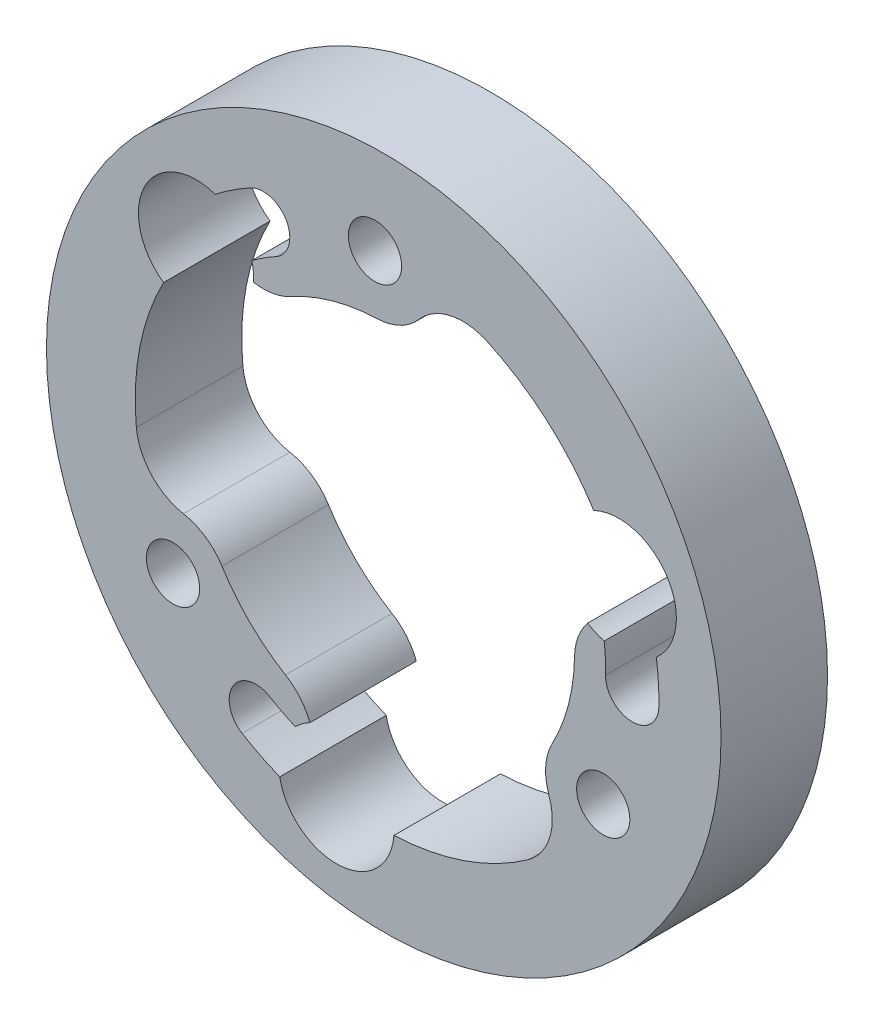
SolidWorks part; units mm, degrees
ref_plane "Plan de face" through (0, 0, 0) normal (0, 0, 1) x (1, 0, 0)
ref_plane "Plan de dessus" through (0, 0, 0) normal (0, 1, 0) x (1, 0, 0)
ref_plane "Plan de droite" through (0, 0, 0) normal (1, 0, 0) x (0, 0, -1)
sketch "Esquisse1" plane through (0, 0, 0) normal (0, 0, 1) x (1, 0, 0)
  line L0 (-0.4938, 13.9913) -> (-11.8699, -7.4233) construction
  line L1 (-11.8699, -7.4233) -> (12.3637, -6.568) construction
  line L2 (12.3637, -6.568) -> (-0.4938, 13.9913) construction
  circle A0 centre (0, 0) radius 19
  circle A2 centre (-0.4938, 13.9913) radius 1.5
  arc A12 (-0.3792, 10.7433) -> (1.9825, 11.8865) centre (-0.4938, 13.9913) ccw
  arc A16 (5.8069, 12.7389) -> (1.9825, 11.8865) centre (4.4589, 9.7817) ccw
  arc A18 (-12.4014, 6.4965) -> (-13.9357, -1.3405) centre (0, 0) ccw
  arc A27 (0.5746, -13.9882) -> (8.1288, -11.3984) centre (0, 0) ccw
  arc A28 (11.8268, 7.4917) -> (5.8069, 12.7389) centre (0, 0) ccw
  arc A30 (-6.0642, 10.9305) -> (-7.5196, 13.5538) centre (-6.7919, 12.2421) ccw
  arc A31 (-7.3226, 9.0358) -> (-5.2152, 9.4002) centre (-6.7919, 12.2421) ccw
  circle A34 centre (-0.4938, 13.9913) radius 3.25 construction
  arc A35 (-7.3226, 9.0358) -> (-10.0387, 12.3873) centre (-6.7919, 12.2421) ccw construction
  arc A36 (-0.6094, 13.9867) -> (-1.9502, 13.6321) centre (-0.4679, 10.7398) ccw [skipped]
  arc A38 (-0.3792, 10.7433) -> (-5.2152, 9.4002) centre (0, 0) ccw
  arc A41 (-7.3226, 9.0358) -> (-7.4369, 10.047) centre (-10.5694, 9.1809) ccw
  arc A47 (-9.4978, 12.2492) -> (-12.4014, 6.4965) centre (-10.5694, 9.1809) ccw
  arc A48 (-11.4901, 7.9967) -> (-9.0762, 9.3245) centre (-10.5694, 9.1809) ccw [skipped]
  arc A49 (-10.4896, 5.9319) -> (-8.1158, 7.0496) centre (-10.5694, 9.1809) ccw [skipped]
  arc A51 (-7.5196, 13.5538) -> (-9.4978, 12.2492) centre (0, 0) ccw
  arc A52 (-6.0642, 10.9305) -> (-7.4369, 10.047) centre (0, 0) ccw
  circle A53 centre (12.3637, -6.568) radius 1.5
  arc A54 (9.4936, -5.0433) -> (9.3027, -7.6602) centre (12.3637, -6.568) ccw
  arc A55 (8.1288, -11.3984) -> (9.3027, -7.6602) centre (6.2417, -8.7523) ccw
  arc A56 (12.4982, -0.2135) -> (15.4977, -0.2647) centre (13.998, -0.2391) ccw
  arc A57 (11.4865, 1.8237) -> (10.7484, -0.1836) centre (13.998, -0.2391) ccw
  arc A58 (9.4936, -5.0433) -> (10.7484, -0.1836) centre (0, 0) ccw
  arc A59 (11.4865, 1.8237) -> (12.4194, 1.417) centre (13.2356, 4.5629) ccw
  arc A61 (15.357, 2.1008) -> (11.8268, 7.4917) centre (13.2356, 4.5629) ccw
  arc A62 (15.4977, -0.2647) -> (15.357, 2.1008) centre (0, 0) ccw
  arc A63 (12.4982, -0.2135) -> (12.4194, 1.417) centre (0, 0) ccw
  circle A64 centre (12.3637, -6.568) radius 3.25 construction
  arc A65 (11.4865, 1.8237) -> (15.747, 2.5001) centre (13.998, -0.2391) ccw construction
  circle A66 centre (-11.8699, -7.4233) radius 1.5
  arc A67 (-9.1144, -5.7) -> (-11.2853, -4.2263) centre (-11.8699, -7.4233) ccw
  arc A68 (-13.9357, -1.3405) -> (-11.2853, -4.2263) centre (-10.7006, -1.0293) ccw
  arc A69 (-6.434, -10.717) -> (-7.9781, -13.2891) centre (-7.2061, -12.003) ccw
  arc A70 (-4.1639, -10.8594) -> (-5.5332, -9.2166) centre (-7.2061, -12.003) ccw
  arc A71 (-9.1144, -5.7) -> (-5.5332, -9.2166) centre (0, 0) ccw
  arc A72 (-4.1639, -10.8594) -> (-4.9825, -11.464) centre (-2.6662, -13.7438) ccw
  arc A74 (-5.8592, -14.3499) -> (0.5746, -13.9882) centre (-2.6662, -13.7438) ccw
  arc A75 (-7.9781, -13.2891) -> (-5.8592, -14.3499) centre (0, 0) ccw
  arc A76 (-6.434, -10.717) -> (-4.9825, -11.464) centre (0, 0) ccw
  circle A77 centre (-11.8699, -7.4233) radius 3.25 construction
  arc A78 (-4.1639, -10.8594) -> (-5.7084, -14.8874) centre (-7.2061, -12.003) ccw construction
  arc A79 (-4.0307, 9.9657) -> (-5.2152, 9.4002) centre (0, 0) ccw [skipped]
  point P9 (0, 0)
  point P31 (0, 0)
  point P43 (0, 0)
  point P54 (0, 0)
  point P84 (0, 0)
  dimension "D2" = 3
  dimension "D3" = 3
  dimension "D4" = 2
  dimension "D5" = 2
  dimension "D10" = 14
  dimension "D6" = 60
  dimension "D7" = 60
extrude "Boss.-Extru.2" add sketch "Esquisse1" along normal blind 6
